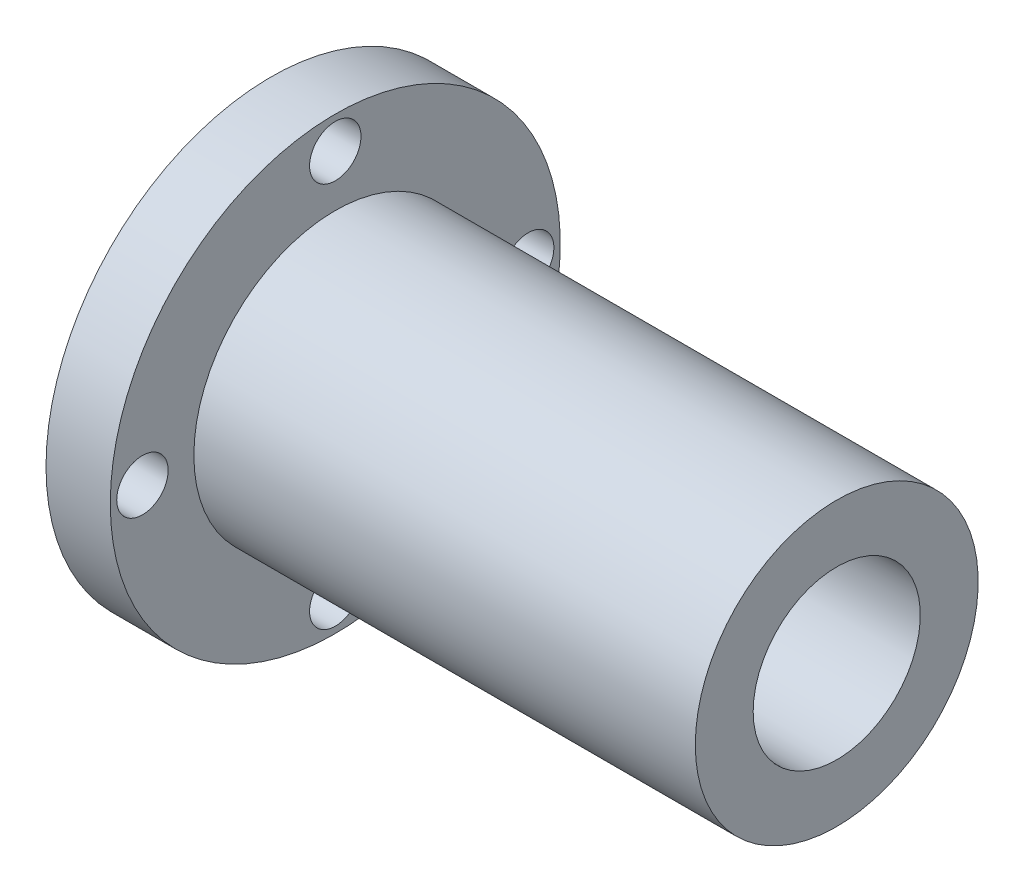
SolidWorks part; units mm, degrees
ref_plane "Plan de face" through (0, 0, 0) normal (0, 0, 1) x (1, 0, 0)
ref_plane "Plan de dessus" through (0, 0, 0) normal (0, 1, 0) x (1, 0, 0)
ref_plane "Plan de droite" through (0, 0, 0) normal (1, 0, 0) x (0, 0, -1)
sketch "Esquisse1" plane through (0, 0, 0) normal (0, 0, 1) x (1, 0, 0)
  line L0 (0, 10) -> (0, 17.5)
  line L1 (0, 17.5) -> (5, 17.5)
  line L2 (5, 17.5) -> (5, 11)
  line L3 (20, 6.5) -> (20, 10)
  line L4 (20, 6.5) -> (44, 6.5)
  line L5 (0, 10) -> (20, 10)
  line L6 (5, 11) -> (44, 11)
  line L7 (44, 6.5) -> (44, 11)
  line L8 (0, 0) -> (34.6007, 0) construction
revolve "Révolution1" add sketch "Esquisse1" angle 360 about L8
sketch "Esquisse2" plane through (0, 0, 0) normal (-1, 0, 0) x (0, 0, 1)
  circle A1 centre (0, 15) radius 2
  circle A2 centre (15, 0) radius 2
  circle A3 centre (0, -15) radius 2
  circle A4 centre (-15, 0) radius 2
extrude "Extrusion1" cut sketch "Esquisse2" against normal through all
